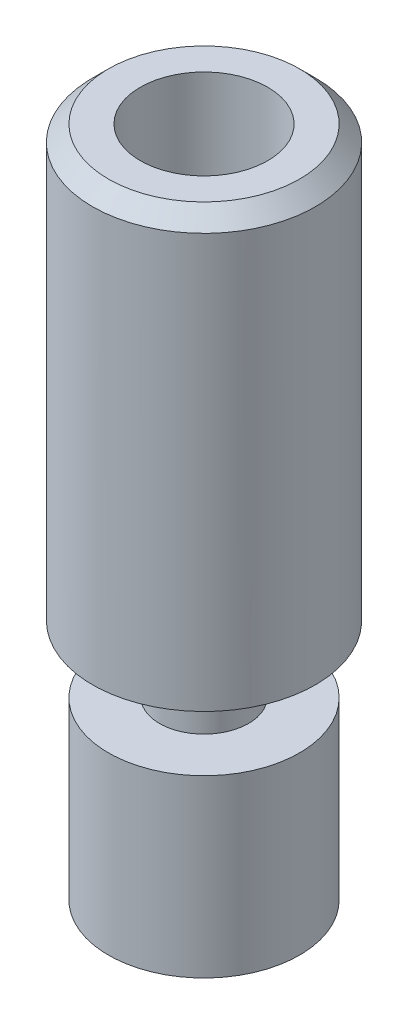
SolidWorks part; units mm, degrees
material "AISI 304"
ref_plane "Front Plane" through (0, 0, 0) normal (0, 0, 1) x (1, 0, 0)
ref_plane "Top Plane" through (0, 0, 0) normal (0, 1, 0) x (1, 0, 0)
ref_plane "Right Plane" through (0, 0, 0) normal (1, 0, 0) x (0, 0, -1)
sketch "Sketch1" plane through (0, 0, 0) normal (0, 0, 1) x (1, 0, 0)
  line L0 (0, -10.55) -> (0, 10.55) construction
  line L1 (1, -10.55) -> (3, -10.55)
  line L2 (3, -10.55) -> (3, -5.05)
  line L3 (3, -5.05) -> (1.4, -5.05)
  line L4 (1.4, -5.05) -> (1.4, -2.95)
  line L5 (1.4, -2.95) -> (3.5, -2.95)
  line L6 (3.5, -2.95) -> (3.5, 10.55)
  line L7 (3.5, 10.55) -> (2, 10.55)
  line L8 (2, 10.55) -> (2, 6.55)
  line L9 (2, 6.55) -> (1, 5.9726)
  line L10 (1, 5.9726) -> (1, -10.55)
  dimension "D2" = 2
  dimension "D3" = 6
  dimension "D4" = 2.8
  dimension "D5" = 7
  dimension "D6" = 4
  dimension "D7" = 4
  dimension "D8" = 13.5
  dimension "D9" = 2.1
  dimension "D10" = 120
  dimension "D11" = 5.5
revolve "Revolve1" add sketch "Sketch1" angle 360 about L0
chamfer "Chamfer1" distance 0.5 angle 45 1 edges at (0, 10.55, -3.5)
